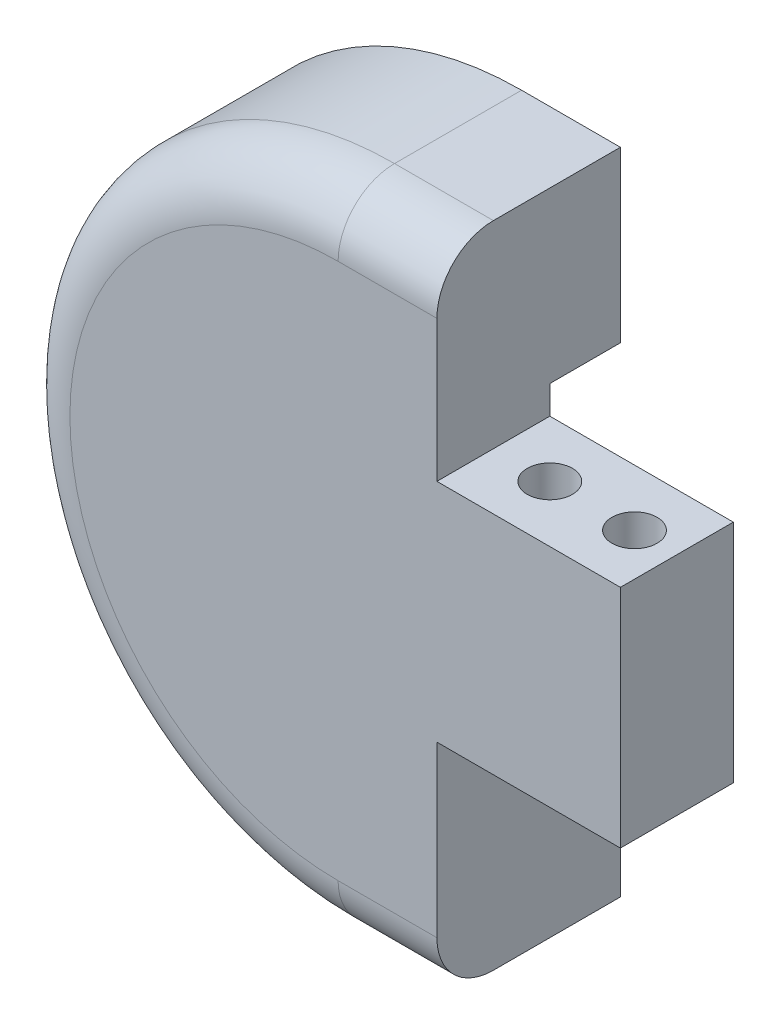
SolidWorks part; units mm, degrees
ref_plane "Front" through (0, 0, 0) normal (0, 0, 1) x (1, 0, 0)
ref_plane "Top" through (0, 0, 0) normal (0, 1, 0) x (1, 0, 0)
ref_plane "Right" through (0, 0, 0) normal (1, 0, 0) x (0, 0, -1)
sketch "Sketch1" plane through (0, 0, 0) normal (0, 0, 1) x (1, 0, 0)
  line L0 (-11, 0) -> (-1, 0) construction
  line L1 (-1, 0) -> (9, 0) construction
  line L2 (3.5, 12) -> (3.5, 5)
  line L3 (3.5, 5) -> (10, 5)
  line L5 (10, -3) -> (3.5, -3)
  line L6 (10, 5) -> (10, -3)
  line L7 (0, 12) -> (3.5, 12)
  line L8 (0, -11) -> (3.5, -11)
  line L9 (3.5, -3) -> (3.5, -11)
  arc A1 (0, 12) -> (0, -11) centre (0, 0.5) ccw
extrude "Boss-Extrude1" add sketch "Sketch1" along normal blind 6.5
sketch "Sketch2" plane through (0, 0, 0) normal (0, 1, 0) x (1, 0, 0)
  line L0 (10, -4.5) -> (8.5, -4.5) construction
  line L2 (8.5, -4.5) -> (5.5, -4.5) construction
  circle A0 centre (8.5, -4.5) radius 0.8
  circle A1 centre (5.5, -4.5) radius 0.8
extrude "Cut-Extrude1" cut sketch "Sketch2" against normal through all from offset 11
fillet "Fillet1" radius 2 3 edges at (1.75, 12, 6.5) (1.75, -11, 6.5) (-11.5, 0.5, 6.5)
sketch "Sketch5" plane through (0, 0, 0) normal (0, 0, 1) x (1, 0, 0)
  line L0 (-5.5, 0.5) -> (0, 0.5) construction
  line L1 (0, 0.5) -> (10, 0.5) construction
  line L2 (0, 0.5) -> (0, 6) construction
  line L3 (0, 0.5) -> (0, -5) construction
  line L4 (-5.5, -1) -> (-4, -1) construction
  line L5 (-4, -1) -> (-4, -4) construction
  line L6 (-5.5, -1) -> (-4, -4)
  line L7 (-4, -4) -> (-4, -5)
  line L8 (-4, -5) -> (0, -5)
  line L9 (0, -5) -> (4.25, -5)
  line L10 (4.25, -5) -> (4.25, -4)
  line L11 (4.25, -4) -> (10, -4)
  line L12 (10, -4) -> (10, 0.5)
  line L13 (-5.5, 2) -> (-4, 2) construction
  line L14 (-4, 2) -> (-4, 5) construction
  line L15 (-5.5, 2) -> (-4, 5)
  line L16 (-4, 5) -> (-4, 6)
  line L17 (-4, 6) -> (0, 6)
  line L18 (0, 6) -> (4.25, 6)
  line L19 (4.25, 6) -> (4.25, 5)
  line L20 (4.25, 5) -> (10, 5)
  line L21 (10, 5) -> (10, 0.5)
  line L22 (0, 5.5) -> (0, 0.5) construction
  line L23 (-5.5, 2) -> (-5.5, 0.5)
  line L24 (-5.5, 0.5) -> (-5.5, -1)
  line L25 (0, -4.5) -> (0, 0.5) construction
extrude "Pot Insert" cut sketch "Sketch5" along normal blind 2.5
sketch "Sketch6" plane through (0, 0, 0) normal (0, 0, 1) x (1, 0, 0)
  circle A0 centre (0, 0) radius 2.75
extrude "Pot Hole" cut sketch "Sketch6" along normal blind 1.5 from offset 2.5
